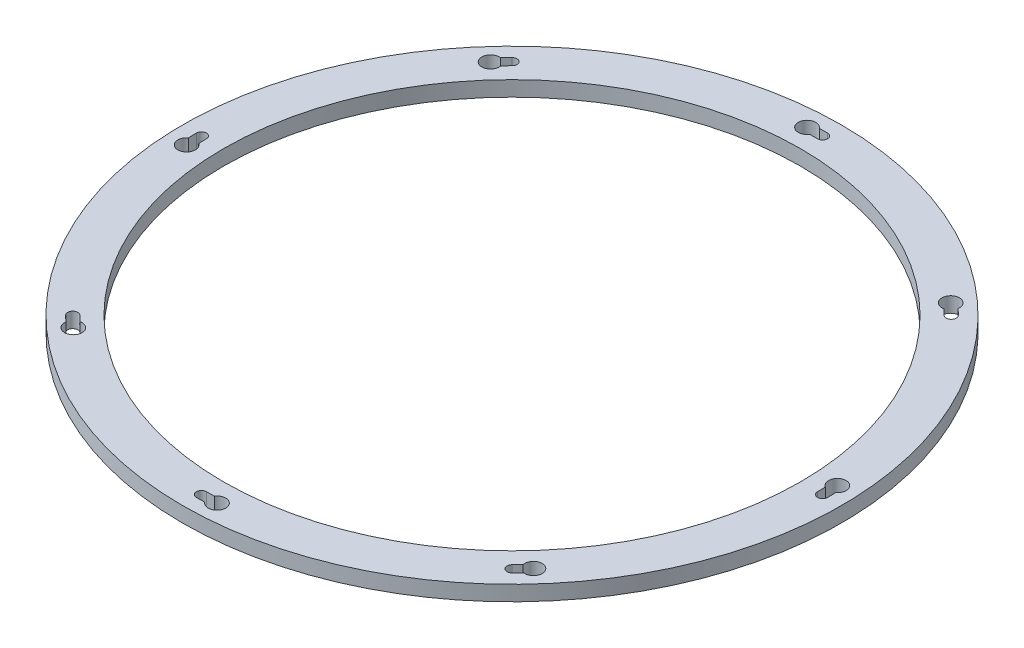
SolidWorks part; units mm, degrees
material "6061 Alloy"
ref_plane "Front Plane" through (0, 0, 0) normal (0, 0, 1) x (1, 0, 0)
ref_plane "Top Plane" through (0, 0, 0) normal (0, 1, 0) x (1, 0, 0)
ref_plane "Right Plane" through (0, 0, 0) normal (1, 0, 0) x (0, 0, -1)
sketch "Sketch1" plane through (0, 0, 0) normal (0, 1, 0) x (1, 0, 0)
  circle A0 centre (0, 0) radius 190
  circle A1 centre (0, 0) radius 217
  circle A2 centre (0, 0) radius 206 construction
  circle A3 centre (0, 206) radius 2.75 construction
  dimension "D1" = 380
  dimension "D2" = 5.5
  dimension "D3" = 16
  dimension "D4" = 11
extrude "MainRing" add sketch "Sketch1" along normal blind 10
hole_wizard "M6 Clearance Hole1" positions "Sketch2" profile "Sketch4" hole size "M6" standard "ISO" end condition through all
sketch "Sketch2" plane through (0, 0, 0) normal (0, -1, 0) x (-1, 0, 0)
  line L0 (0, -217) -> (0, -190) construction
  circle A0 centre (0, 0) radius 217 construction
  circle A1 centre (0, 0) radius 190 construction
  point P0 (0, -204.5)
  point P14 (0, -203.5)
  dimension "D1" = 1
sketch "Sketch4" plane through (0, 0, 204.5) normal (1, 0, 0) x (0, 0, -1)
  line L0 (0, 0) -> (0, 10)
  line L1 (0, 10) -> (3.3, 10)
  line L2 (3.3, 10) -> (3.3, 0)
  line L5 (3.3, 0) -> (0, 0)
  line L11 (0, -6.35) -> (0, 107.95) construction
  dimension "Thru Hole Dia." = 6.6
  dimension "Thru Hole Depth" = 10
pattern_circular "HolePattern" count 8 over 360 about axis through (0, 0, 0) along (0, 1, 0) of "M6 Clearance Hole1"
sketch "Sketch5" plane through (0, 0, 0) normal (0, -1, 0) x (1, 0, 0)
  arc A0 (201.1336, -5.1683) -> (207.7294, -5.4151) centre (204.2555, -9.997) ccw
  circle A1 centre (0, 0) radius 204.5 construction
  circle A2 centre (204.5, 0) radius 3.3 construction
  circle A3 centre (0, 0) radius 190 construction
  arc A4 (201.2, 0) -> (201.1336, -5.1683) centre (0, 0) cw
  arc A5 (207.8, 0) -> (207.7294, -5.4151) centre (0, 0) cw
  arc A6 (201.2, 0) -> (207.8, 0) centre (204.5, 0) ccw
  point P10 (204.5, 0)
  dimension "D1" = 11.5
  dimension "D2" = 10
extrude "Cut-Extrude1" cut sketch "Sketch5" against normal through all
pattern_circular "CirPattern1" count 8 over 360 about axis through (0, 0, 0) along (0, 1, 0) of "Cut-Extrude1"
